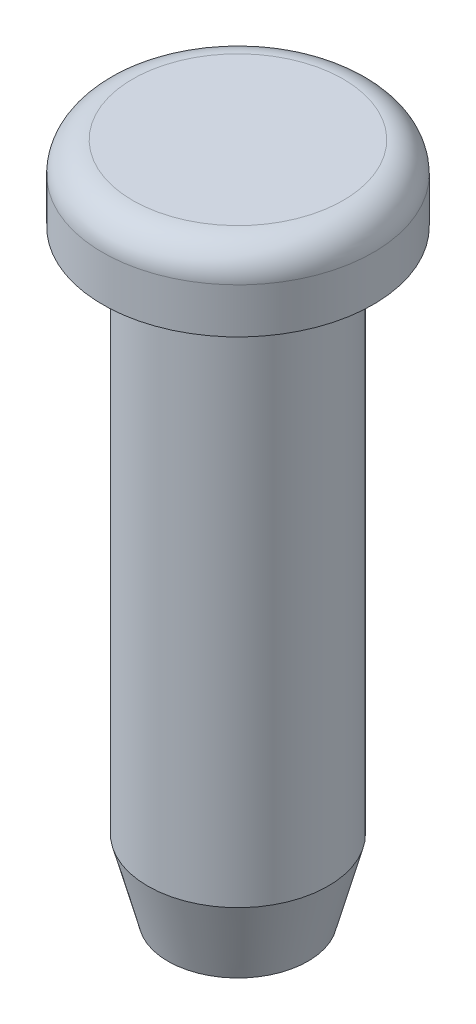
SolidWorks part; units mm, degrees
material "Plain Carbon Steel"
ref_plane "Front Plane" through (0, 0, 0) normal (0, 0, 1) x (1, 0, 0)
ref_plane "Top Plane" through (0, 0, 0) normal (0, 1, 0) x (1, 0, 0)
ref_plane "Right Plane" through (0, 0, 0) normal (1, 0, 0) x (0, 0, -1)
sketch "Sketch1" plane through (0, 0, 0) normal (0, 1, 0) x (1, 0, 0)
  circle A0 centre (0, 0) radius 1.524
  dimension "D1" = 3.048
extrude "Boss-Extrude1" add sketch "Sketch1" along normal mid plane 10.16
chamfer "Chamfer1" distance 1.27 angle 15 1 edges at (0, -5.08, 1.524)
sketch "Sketch2" plane through (0, 0, 0) normal (0, 0, 1) x (1, 0, 0)
  line L0 (1.524, 5.08) -> (-1.524, 5.08) construction
  line L1 (0, 5.08) -> (2.286, 5.08)
  line L2 (0, 5.08) -> (0, 6.35)
  line L3 (0, 6.35) -> (1.778, 6.35)
  line L4 (2.286, 5.08) -> (2.286, 5.842)
  arc A0 (1.778, 6.35) -> (2.286, 5.842) centre (1.778, 5.842) cw
  point P9 (2.286, 6.35)
  dimension "D3" = 0.508
  dimension "D1" = 1.27
  dimension "D2" = 2.286
revolve "Revolve1" add sketch "Sketch2" angle 360 about L2
